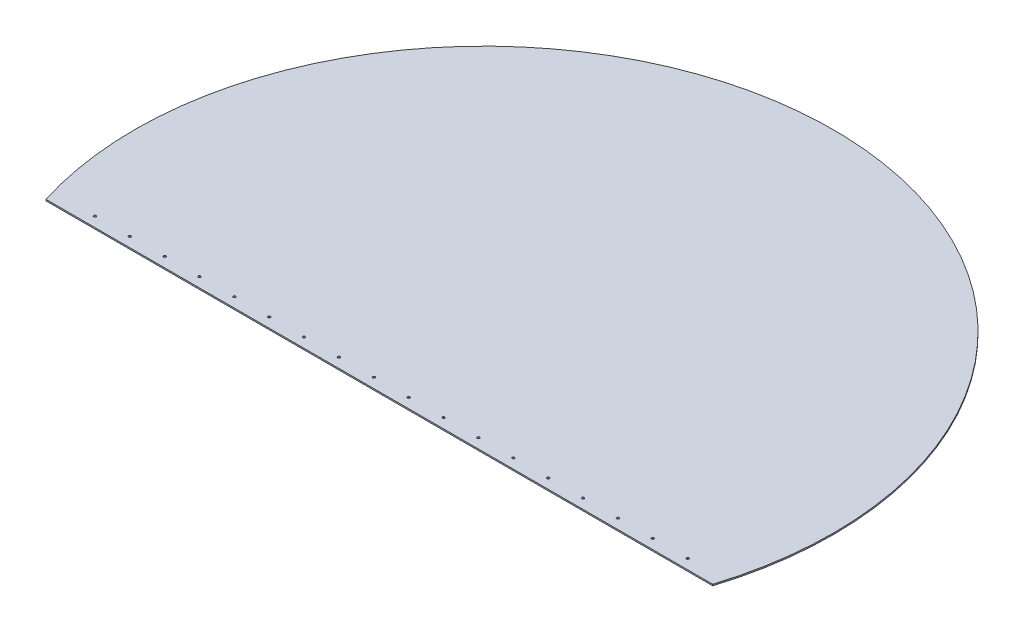
SolidWorks part; units mm, degrees
material "Wrought Stainless Steel"
ref_plane "Front Plane" through (0, 0, 0) normal (0, 0, 1) x (1, 0, 0)
ref_plane "Top Plane" through (0, 0, 0) normal (0, 1, 0) x (1, 0, 0)
ref_plane "Right Plane" through (0, 0, 0) normal (1, 0, 0) x (0, 0, -1)
sketch "Sketch1" plane through (0, 0, 0) normal (0, 1, 0) x (1, 0, 0)
  line L0 (-485.6394, -152.4) -> (485.6394, -152.4)
  arc A0 (485.6394, -152.4) -> (-485.6394, -152.4) centre (0, 0) ccw
  dimension "D2" = 508.9906
  dimension "D1" = 152.4
extrude "Boss-Extrude1" add sketch "Sketch1" along normal blind 1.9837
sketch "Sketch2" plane through (0, 1.9837, 0) normal (0, 1, 0) x (1, 0, 0)
  line L0 (-485.6394, -152.4) -> (485.6394, -152.4) construction
  circle A0 centre (434.8394, -138.1125) radius 1.778
  dimension "D1" = 14.2875
  dimension "D2" = 3.556
  dimension "D3" = 50.8
extrude "Cut-Extrude1" cut sketch "Sketch2" against normal blind 3.175
pattern_linear "LPattern1" count 18 spacing 50.8 along (-1, 0, 0) of "Cut-Extrude1"
